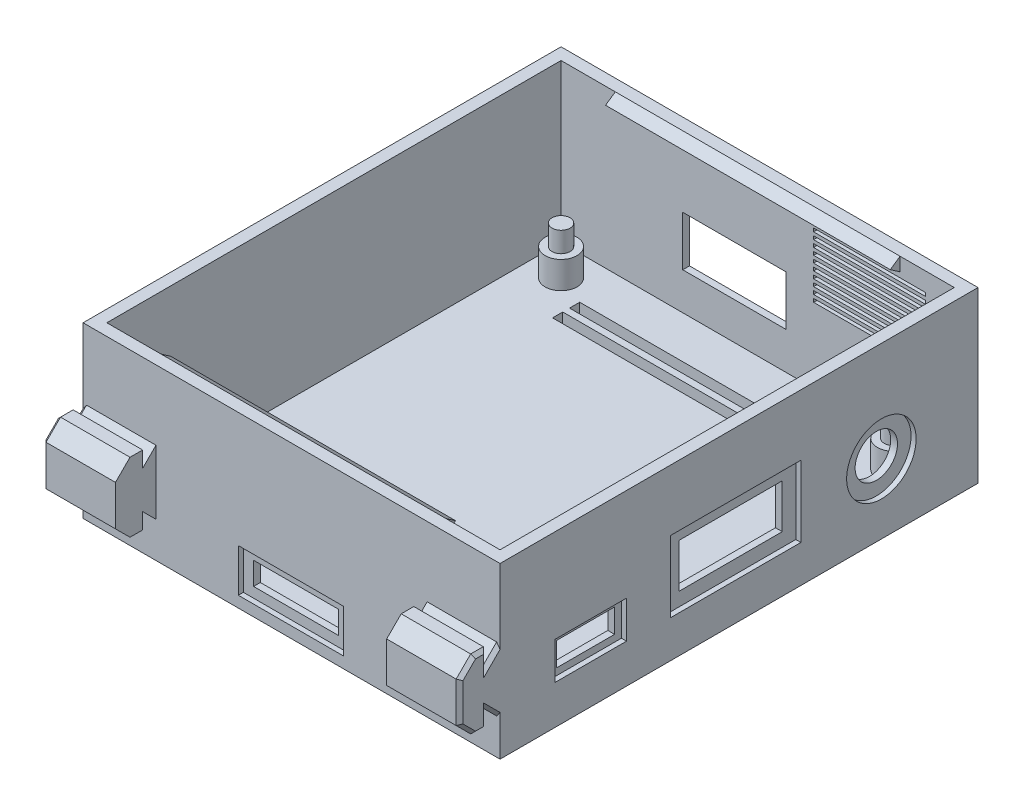
SolidWorks part; units mm, degrees
ref_plane "Front Plane" through (0, 0, 0) normal (0, 0, 1) x (1, 0, 0)
ref_plane "Top Plane" through (0, 0, 0) normal (0, 1, 0) x (1, 0, 0)
ref_plane "Right Plane" through (0, 0, 0) normal (1, 0, 0) x (0, 0, -1)
sketch "Sketch1" plane through (0, 0, 0) normal (0, 1, 0) x (1, 0, 0)
  line L0 (0, 0) -> (0, 50000) construction
  line L1 (-28, -32.5) -> (28, -32.5) construction
  line L2 (-28, -32.5) -> (-28, 32.5) construction
  line L3 (-28, 32.5) -> (28, 32.5) construction
  line L4 (28, -32.5) -> (28, 32.5) construction
  line L5 (-28, -32.5) -> (28, 32.5) construction
  line L6 (-28, 32.5) -> (28, -32.5) construction
  line L7 (0, 0) -> (-50000, 0) construction
  line L8 (-29, 33.5) -> (29, 33.5)
  line L9 (29, -33.5) -> (29, 33.5)
  line L10 (-29, -33.5) -> (29, -33.5)
  line L11 (-29, -33.5) -> (-29, 33.5)
  line L12 (-30.75, 35.25) -> (30.75, 35.25)
  line L13 (30.75, -35.25) -> (30.75, 35.25)
  line L14 (-30.75, -35.25) -> (30.75, -35.25)
  line L15 (-30.75, -35.25) -> (-30.75, 35.25)
  circle A0 centre (-24.5, 29) radius 1.35 construction
  circle A1 centre (24.5, 29) radius 1.35 construction
  circle A2 centre (-24.5, -29) radius 1.35 construction
  circle A3 centre (24.5, -29) radius 1.35 construction
  point P0 (0, 0)
  dimension "D3" = 58
  dimension "D4" = 49
  dimension "D5" = 2.7
  dimension "D1" = 56
  dimension "D2" = 65
  dimension "D6" = 1
  dimension "D7" = 1.75
extrude "Boss-Extrude1" add sketch "Sketch1" along normal blind 25
sketch "Sketch2" plane through (0, 0, 0) normal (0, 1, 0) x (1, 0, 0)
  line L8 (-30.75, -35.25) -> (30.75, -35.25) construction
  line L9 (30.75, -35.25) -> (30.75, 35.25) construction
  line L10 (30.75, 35.25) -> (-30.75, 35.25) construction
  line L11 (-30.75, 35.25) -> (-30.75, -35.25) construction
  line L12 (-30.75, -35.25) -> (30.75, -35.25)
  line L13 (30.75, -35.25) -> (30.75, 35.25)
  line L14 (30.75, 35.25) -> (-30.75, 35.25)
  line L15 (-30.75, 35.25) -> (-30.75, -35.25)
extrude "Boss-Extrude5" add sketch "Sketch2" along normal blind 1.75
sketch "Sketch3" plane through (0, 1.75, 0) normal (0, 1, 0) x (1, 0, 0)
  circle A0 centre (24.5, -29) radius 1.35 construction
  circle A1 centre (-24.5, -29) radius 1.35 construction
  circle A2 centre (-24.5, 29) radius 1.35 construction
  circle A3 centre (24.5, 29) radius 1.35 construction
  circle A30 centre (24.5, -29) radius 1.35 construction
  circle A31 centre (-24.5, -29) radius 1.35 construction
  circle A32 centre (-24.5, 29) radius 1.35 construction
  circle A33 centre (24.5, 29) radius 1.35 construction
  circle A34 centre (-24.5, 29) radius 2.35
  circle A35 centre (24.5, 29) radius 2.35
  circle A36 centre (24.5, -29) radius 2.35
  circle A37 centre (-24.5, -29) radius 2.35
  dimension "D1" = 1
extrude "Boss-Extrude2" add sketch "Sketch3" along normal blind 4
sketch "Sketch4" plane through (0, 5.75, 0) normal (0, 1, 0) x (1, 0, 0)
  line L2 (0, 0) -> (50000, 0) construction
  line L3 (0, 0) -> (0, 50000) construction
  circle A0 centre (-24.5, 29) radius 1.35 construction
  circle A1 centre (-24.5, 29) radius 1.35 construction
  circle A2 centre (-24.5, 29) radius 1.325
  circle A3 centre (24.5, 29) radius 1.325
  circle A4 centre (24.5, -29) radius 1.325
  circle A5 centre (-24.5, -29) radius 1.325
  dimension "D1" = 0.025
extrude "Boss-Extrude3" add sketch "Sketch4" along normal blind 3
sketch "Sketch5" plane through (30.75, 0, 0) normal (1, 0, 0) x (0, 0, -1)
  line L1 (32.5, 7.4129) -> (32.5, 34.249) construction
  line L2 (31.35, 5.75) -> (26.65, 5.75) construction
  line L3 (31.35, 5.75) -> (26.65, 5.75)
  line L4 (-26.15, 6.75) -> (-17.6, 6.75)
  line L5 (35.25, 25) -> (35.25, 0) construction
  line L6 (22.15, 5.75) -> (-49977.85, 5.75) construction
  line L8 (-8.125, 14) -> (7.125, 14)
  line L9 (-8.125, 14) -> (-8.125, 7.5)
  line L10 (-8.125, 7.5) -> (7.125, 7.5)
  line L11 (7.125, 14) -> (7.125, 7.5)
  line L12 (-8.125, 14) -> (7.125, 7.5) construction
  line L13 (-8.125, 7.5) -> (7.125, 14) construction
  line L14 (-26.15, 6.75) -> (-26.15, 10.25)
  line L15 (-26.15, 10.25) -> (-17.6, 10.25)
  line L16 (-17.6, 6.75) -> (-17.6, 10.25)
  line L17 (-26.15, 6.75) -> (-17.6, 10.25) construction
  line L18 (-26.15, 10.25) -> (-17.6, 6.75) construction
  line L20 (-32.5, 25) -> (-32.5, 0)
  line L21 (-32.5, 25) -> (-32.5, 0) construction
  circle A0 centre (21, 10.24) radius 3.125
  circle A1 centre (21, 10.24) radius 1.875 construction
  circle A2 centre (21, 10.24) radius 1.875 construction
  point P6 (-21.875, 8.5)
  point P8 (-0.5, 10.75)
  dimension "D2" = 6.25
  dimension "D5" = 2.75
  dimension "D4" = 7.615
  dimension "D6" = 32
  dimension "D7" = 15.25
  dimension "D8" = 6.5
  dimension "D9" = 8.25
  dimension "D10" = 2.75
  dimension "D11" = 10.625
  dimension "D12" = 3.5
  dimension "D13" = 4.5
  dimension "D14" = 8.55
extrude "Cut-Extrude2" cut sketch "Sketch5" against normal up to next contours A0 | L14 L4 L16 L15 | L9 L8 L11 L10
sketch "Sketch7" plane through (0, 0, 0) normal (1, 0, 0) x (0, 0, -1)
  line L0 (-35.25, 25) -> (-35.25, 0) construction
  line L1 (-35.25, 14.73) -> (-35.25, 5.27)
  line L2 (-35.25, 14.73) -> (-37.22, 12.76)
  line L3 (-37.22, 12.76) -> (-37.22, 15.11)
  line L4 (-37.22, 15.11) -> (-39.08, 15.11)
  line L5 (-39.08, 15.11) -> (-41.22, 12.97)
  line L6 (-41.22, 12.97) -> (-41.22, 7.03)
  line L7 (-35.25, 10) -> (-50035.25, 10) construction
  line L8 (-39.08, 4.89) -> (-41.22, 7.03)
  line L9 (-37.22, 4.89) -> (-39.08, 4.89)
  line L10 (-37.22, 7.24) -> (-37.22, 4.89)
  line L11 (-35.25, 5.27) -> (-37.22, 7.24)
  line L12 (-200000, 0) -> (250000, 0) construction
  point P13 (-41.22, 10)
  dimension "D1" = 45
  dimension "D2" = 2.97
  dimension "D3" = 1.97
  dimension "D4" = 1.86
  dimension "D5" = 5.11
  dimension "D6" = 2.35
  dimension "D7" = 45
  dimension "D8" = 10
extrude "Boss-Extrude4" add sketch "Sketch7" along normal up to surface and the other way up to surface up to face at (30.75, 10.24, -24.125) other way up to face at (-30.75, 12.5, 0)
sketch "Sketch8" plane through (0, 0, 0) normal (0, 1, 0) x (1, 0, 0)
  line L0 (-30.75, -35.25) -> (30.75, -35.25) construction
  line L1 (-20, -35.25) -> (20, -35.25)
  line L2 (-20, -35.25) -> (-20, -41.22)
  line L3 (-20, -41.22) -> (20, -41.22)
  line L4 (20, -35.25) -> (20, -41.22)
  line L5 (30.75, -41.22) -> (-30.75, -41.22) construction
  line L6 (-30.75, -41.22) -> (-30.75, -39.08) construction
  point P8 (0, -35.25)
  dimension "D1" = 40
  dimension "D2" = 10.75
extrude "Cut-Extrude3" cut sketch "Sketch8" along normal up to surface (10.22 mm away) from surface at 4.89 up to face at (0, 15.11, 38.15) starting at face at (0, 4.89, 38.15)
sketch "Sketch10" plane through (0, 0, -35.25) normal (0, 0, -1) x (-1, 0, 0)
  line L0 (10.8, 7.24) -> (10.8, 14.34) construction
  line L5 (-3.9, 7.24) -> (-3.9, 14.34) construction
  line L6 (-3.9, 14.34) -> (10.8, 14.34) construction
  line L7 (10.8, 7.24) -> (10.8, 14.34) construction
  line L8 (-3.9, 7.24) -> (-3.9, 14.34) construction
  line L9 (-3.9, 14.34) -> (10.8, 14.34) construction
  line L10 (-4.15, 7.24) -> (-4.15, 14.59)
  line L11 (-4.15, 14.59) -> (11.05, 14.59)
  line L12 (11.05, 7.24) -> (11.05, 14.59)
  line L13 (-4.15, 7.24) -> (11.05, 7.24)
  line L14 (-24.5, 12.75) -> (-8.5, 12.75) construction
  line L15 (-24.5, 12.75) -> (-8.5, 12.75) construction
  line L16 (-25, 7.24) -> (25, 7.24) construction
  line L17 (-25, 7.24) -> (25, 7.24) construction
  line L18 (-16.5, 12.75) -> (-16.5, 31.73) construction
  line L19 (-24.75, 22.24) -> (-8.25, 22.24)
  line L20 (-24.75, 22.24) -> (-24.75, 21.74)
  line L21 (-24.75, 21.74) -> (-8.25, 21.74)
  line L22 (-8.25, 22.24) -> (-8.25, 21.74)
  line L23 (-24.75, 21.24) -> (-8.25, 21.24)
  line L24 (-24.75, 21.24) -> (-24.75, 20.74)
  line L25 (-24.75, 20.74) -> (-8.25, 20.74)
  line L26 (-8.25, 21.24) -> (-8.25, 20.74)
  line L27 (-16.5, 11.75) -> (-16.5, 30.73) construction
  line L28 (-24.75, 20.24) -> (-8.25, 20.24)
  line L29 (-24.75, 20.24) -> (-24.75, 19.74)
  line L30 (-24.75, 19.74) -> (-8.25, 19.74)
  line L31 (-8.25, 20.24) -> (-8.25, 19.74)
  line L32 (-16.5, 10.75) -> (-16.5, 29.73) construction
  line L33 (-24.75, 19.24) -> (-8.25, 19.24)
  line L34 (-24.75, 19.24) -> (-24.75, 18.74)
  line L35 (-24.75, 18.74) -> (-8.25, 18.74)
  line L36 (-8.25, 19.24) -> (-8.25, 18.74)
  line L37 (-16.5, 9.75) -> (-16.5, 28.73) construction
  line L38 (-24.75, 18.24) -> (-8.25, 18.24)
  line L39 (-24.75, 18.24) -> (-24.75, 17.74)
  line L40 (-24.75, 17.74) -> (-8.25, 17.74)
  line L41 (-8.25, 18.24) -> (-8.25, 17.74)
  line L42 (-16.5, 8.75) -> (-16.5, 27.73) construction
  line L43 (-24.75, 17.24) -> (-8.25, 17.24)
  line L44 (-24.75, 17.24) -> (-24.75, 16.74)
  line L45 (-24.75, 16.74) -> (-8.25, 16.74)
  line L46 (-8.25, 17.24) -> (-8.25, 16.74)
  line L47 (-16.5, 7.75) -> (-16.5, 26.73) construction
  line L48 (-24.75, 16.24) -> (-8.25, 16.24)
  line L49 (-24.75, 16.24) -> (-24.75, 15.74)
  line L50 (-24.75, 15.74) -> (-8.25, 15.74)
  line L51 (-8.25, 16.24) -> (-8.25, 15.74)
  line L52 (-16.5, 6.75) -> (-16.5, 25.73) construction
  line L53 (-24.75, 15.24) -> (-8.25, 15.24)
  line L54 (-24.75, 15.24) -> (-24.75, 14.74)
  line L55 (-24.75, 14.74) -> (-8.25, 14.74)
  line L56 (-8.25, 15.24) -> (-8.25, 14.74)
  line L57 (-16.5, 5.75) -> (-16.5, 24.73) construction
  line L58 (-24.75, 14.24) -> (-8.25, 14.24)
  line L59 (-24.75, 14.24) -> (-24.75, 13.74)
  line L60 (-24.75, 13.74) -> (-8.25, 13.74)
  line L61 (-8.25, 14.24) -> (-8.25, 13.74)
  line L62 (-16.5, 4.75) -> (-16.5, 23.73) construction
  line L63 (-24.75, 13.24) -> (-8.25, 13.24)
  line L64 (-24.75, 13.24) -> (-24.75, 12.74)
  line L65 (-24.75, 12.74) -> (-8.25, 12.74)
  line L66 (-8.25, 13.24) -> (-8.25, 12.74)
  line L67 (-16.5, 3.75) -> (-16.5, 22.73) construction
  point P18 (-16.5, 22.24)
  dimension "D2" = 16.5
  dimension "D3" = 15
  dimension "D4" = 0.5
  dimension "D6" = 0.5
  dimension "D1" = 0.25
  dimension "D5" = 10
extrude "Cut-Extrude4" cut sketch "Sketch10" against normal up to next
sketch "Sketch13" plane through (0, 0, 35.25) normal (0, 0, 1) x (1, 0, 0)
  line L0 (0, 0) -> (0, 27.5) construction
  line L1 (-6.355, 6.49) -> (6.145, 6.49)
  line L2 (-6.355, 6.49) -> (-6.355, 3.14)
  line L3 (-6.355, 3.14) -> (6.145, 3.14)
  line L4 (6.145, 6.49) -> (6.145, 3.14)
  line L5 (-30.75, 0) -> (30.75, 0) construction
  line L6 (-30.75, 10) -> (30.75, 10) construction
  line L7 (-30.75, 7.03) -> (-30.75, 12.97) construction
  line L8 (30.75, 7.03) -> (30.75, 12.97) construction
  line L9 (-25, 7.24) -> (25, 7.24) construction
  line L10 (-25, 7.24) -> (25, 7.24) construction
  line L11 (-6.1, 5.74) -> (-6.1, 4.29) construction
  line L12 (5.89, 5.74) -> (5.89, 4.29) construction
  dimension "D1" = 4.1
  dimension "D2" = 0.75
  dimension "D3" = 12.5
  dimension "D4" = 0.255
  dimension "D5" = 0.255
extrude "Cut-Extrude6" cut sketch "Sketch13" against normal up to next
sketch "Sketch14" plane through (30.75, 0, 0) normal (1, 0, 0) x (0, 0, -1)
  line L24 (-16.6, 5.75) -> (-16.6, 11.25)
  line L25 (-27.15, 5.75) -> (-16.6, 5.75)
  line L26 (-27.15, 11.25) -> (-27.15, 5.75)
  line L27 (-16.6, 11.25) -> (-27.15, 11.25)
  line L28 (-16.6, 5.75) -> (-16.6, 11.25)
  line L29 (-27.15, 5.75) -> (-16.6, 5.75)
  line L30 (-27.15, 11.25) -> (-27.15, 5.75)
  line L31 (-16.6, 11.25) -> (-27.15, 11.25)
  line L46 (-10.125, 5.5) -> (9.125, 5.5)
  line L47 (9.125, 5.5) -> (9.125, 16)
  line L48 (9.125, 16) -> (-10.125, 16)
  line L49 (-10.125, 16) -> (-10.125, 5.5)
  line L50 (-10.125, 5.5) -> (9.125, 5.5)
  line L51 (9.125, 5.5) -> (9.125, 16)
  line L52 (9.125, 16) -> (-10.125, 16)
  line L53 (-10.125, 16) -> (-10.125, 5.5)
  arc A2 (26.125, 10.24) -> (26.125, 10.24) centre (21, 10.24) ccw
  circle A3 centre (21, 10.24) radius 5.125
  dimension "D1" = 1
  dimension "D2" = 2
  dimension "D3" = 2
extrude "Cut-Extrude7" cut sketch "Sketch14" against normal blind 0.75
sketch "Sketch15" plane through (0, 0, -35.25) normal (0, 0, -1) x (-1, 0, 0)
  line L8 (-5.65, 16.09) -> (-5.65, 5.74)
  line L9 (12.55, 16.09) -> (-5.65, 16.09)
  line L10 (12.55, 5.74) -> (12.55, 16.09)
  line L11 (-5.65, 5.74) -> (12.55, 5.74)
  line L12 (-5.65, 16.09) -> (-5.65, 5.74)
  line L13 (12.55, 16.09) -> (-5.65, 16.09)
  line L14 (12.55, 5.74) -> (12.55, 16.09)
  line L15 (-5.65, 5.74) -> (12.55, 5.74)
  dimension "D1" = 1.5
extrude "Cut-Extrude8" cut sketch "Sketch15" against normal blind 0.75
sketch "Sketch17" plane through (0, 0, 35.25) normal (0, 0, 1) x (1, 0, 0)
  line L8 (-7.855, 7.99) -> (-7.855, 1.64)
  line L9 (7.645, 1.64) -> (7.645, 7.99)
  line L10 (-7.855, 1.64) -> (7.645, 1.64)
  line L11 (7.645, 7.99) -> (-7.855, 7.99)
  line L12 (-7.855, 7.99) -> (-7.855, 1.64)
  line L13 (7.645, 1.64) -> (7.645, 7.99)
  line L14 (-7.855, 1.64) -> (7.645, 1.64)
  line L15 (7.645, 7.99) -> (-7.855, 7.99)
  dimension "D1" = 1.5
extrude "Cut-Extrude9" cut sketch "Sketch17" against normal blind 0.75
sketch "Sketch18" plane through (0, 0, 0) normal (1, 0, 0) x (0, 0, -1)
  line L0 (-33.5, 25) -> (-33.5, 1.75) construction
  line L1 (-33.5, 25) -> (-33.5, 1.75) construction
  line L2 (-33.5, 25) -> (-32.0639, 24)
  line L3 (-32.0639, 24) -> (-33.5, 23)
  line L4 (-33.5, 25) -> (-33.5, 23)
  line L5 (0, 0) -> (0, 41.3365) construction
  line L6 (33.5, 25) -> (33.5, 23)
  line L7 (32.0639, 24) -> (33.5, 23)
  line L8 (33.5, 25) -> (32.0639, 24)
  dimension "D1" = 2
  dimension "D2" = 1.75
  dimension "D3" = 1.75
extrude "Boss-Extrude6" add sketch "Sketch18" along normal blind 21 and the other way blind 21
sketch "Sketch19" plane through (0, 0, 0) normal (0, 1, 0) x (1, 0, 0)
  line L0 (0, 0) -> (50000, 0) construction
  line L2 (-20, 27.25) -> (20, 27.25)
  line L3 (-20, 27.25) -> (-20, 25.75)
  line L4 (-20, 25.75) -> (20, 25.75)
  line L5 (20, 27.25) -> (20, 25.75)
  line L6 (-20, 27.25) -> (20, 25.75) construction
  line L7 (-20, 25.75) -> (20, 27.25) construction
  point P3 (0, 26.5)
  point P8 (0, 27.25)
  dimension "D1" = 1.5
  dimension "D2" = 40
  dimension "D3" = 26.5
extrude "Cut-Extrude11" cut sketch "Sketch19" along normal up to next (1.75 mm away)
pattern_linear "LPattern1" count 2 spacing 2.5 along (0, 0, 1) of "Cut-Extrude11"
mirror "Mirror1" about plane through (0, 0, 0) normal (0, 0, 1) of "LPattern1", "Cut-Extrude11"
chamfer "Chamfer1" distance 0.5 angle 45 18 edges at (-30.75, 6.255, 36.235) (30.75, 6.255, 36.235) (-30.75, 13.745, 36.235) (30.75, 13.745, 36.235) (-30.75, 6.065, 37.22) (30.75, 6.065, 37.22) (-30.75, 4.89, 38.15) (30.75, 4.89, 38.15) (-30.75, 5.96, 40.15) (30.75, 5.96, 40.15) (-30.75, 10, 41.22) (30.75, 10, 41.22) (-30.75, 13.935, 37.22) (30.75, 13.935, 37.22) (-30.75, 15.11, 38.15) (30.75, 15.11, 38.15) (-30.75, 14.04, 40.15) (30.75, 14.04, 40.15)
